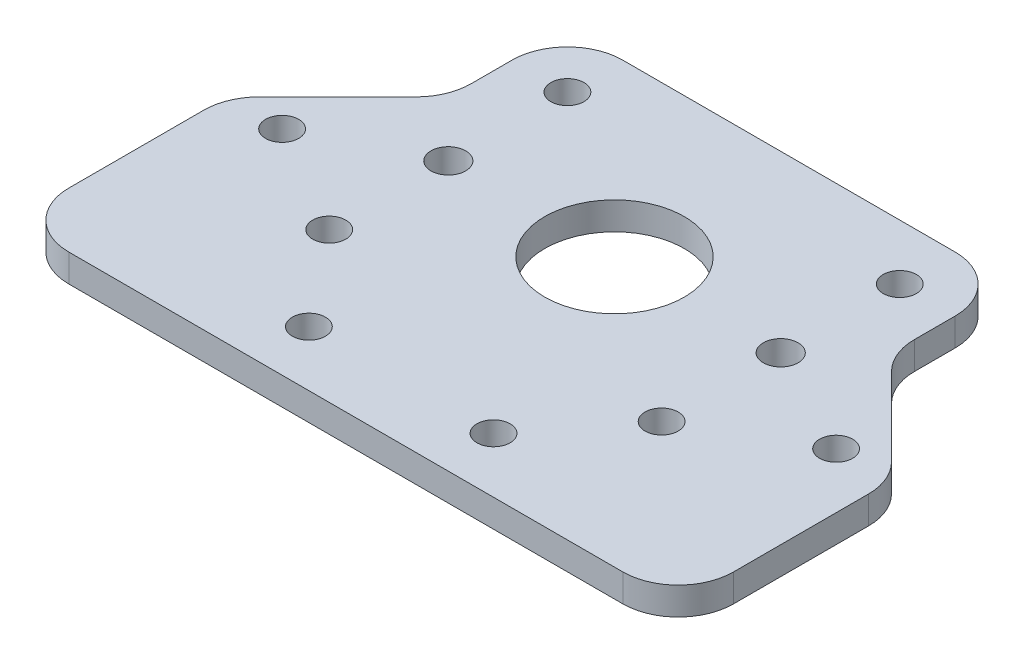
SolidWorks part; units mm, degrees
material "Balsa"
ref_plane "Front" through (0, 0, 0) normal (0, 0, 1) x (1, 0, 0)
ref_plane "Top" through (0, 0, 0) normal (0, 1, 0) x (1, 0, 0)
ref_plane "Right" through (0, 0, 0) normal (1, 0, 0) x (0, 0, -1)
sketch "Sketch1" plane through (0, 0, 0) normal (0, 1, 0) x (1, 0, 0)
  line L0 (38.1, 0) -> (38.1, 200) construction
  line L1 (0, 0) -> (76.2, 0)
  line L2 (0, 0) -> (0, 50.8)
  line L3 (0, 50.8) -> (38.1, 50.8)
  line L4 (38.1, 50.8) -> (76.2, 50.8)
  line L5 (38.1, 38.65) -> (79.051, 38.65) construction
  line L6 (38.1, 37.15) -> (79.051, 37.15) construction
  line L7 (76.2, 50.8) -> (76.2, 0)
  circle A0 centre (38.1, 118.65) radius 80 construction
  circle A1 centre (38.1, 30.8) radius 6.35 construction
  circle A2 centre (38.1, 30.8) radius 20 construction
  circle A4 centre (38.1, 30.8) radius 8
  dimension "D3" = 160
  dimension "D4" = 12.7
  dimension "D5" = 50.8
  dimension "D8" = 16
  dimension "D2" = 40
  dimension "D1" = 1.5
  dimension "D6" = 76.2
extrude "Boss-Extrude1" add sketch "Sketch1" along normal blind 3.175
sketch "Sketch2" plane through (0, 3.175, 0) normal (0, 1, 0) x (1, 0, 0)
  line L0 (38.1, 50.8) -> (38.1, 0) construction
  line L2 (0, 30.8) -> (76.2, 30.8) construction
  line L5 (76.2, 0) -> (76.2, 50.8) construction
  line L6 (76.2, 50.8) -> (0, 50.8) construction
  line L8 (0, 0) -> (76.2, 0) construction
  line L9 (0, 50.8) -> (0, 0) construction
  circle A1 centre (19.05, 30.8) radius 1.9939
  circle A4 centre (57.15, 30.8) radius 1.9939
  point P26 (38.1, 30.8)
  dimension "D1" = 3.9878
  dimension "D2" = 19.05
extrude "Cut-Extrude1" cut sketch "Sketch2" against normal through all
sketch "Sketch14" plane through (0, 0, 0) normal (0, -1, 0) x (1, 0, 0)
  line L0 (38.1, -30.8) -> (3.391, -30.8) construction
  line L2 (38.1, -30.8) -> (38.1, -33.65) construction
  line L3 (19.05, -17.15) -> (57.15, -17.15) construction
  line L5 (57.15, -44.45) -> (19.05, -44.45) construction
  line L7 (76.2, -50.8) -> (0, -50.8) construction
  line L8 (57.15, -30.8) -> (38.1, -30.8) construction
  circle A0 centre (38.1, -30.8) radius 8 construction
  circle A1 centre (57.15, -44.45) radius 1.8986
  circle A2 centre (19.05, -44.45) radius 1.8986
  circle A3 centre (19.05, -17.15) radius 1.8986
  circle A4 centre (57.15, -17.15) radius 1.8986
  circle A5 centre (57.15, -30.8) radius 1.9939 construction
  point P0 (57.15, -44.45)
  point P12 (19.05, -44.45)
  point P13 (19.05, -17.15)
  point P14 (57.15, -17.15)
  dimension "D3" = 3.7973
  dimension "D1" = 19.05
  dimension "D2" = 6.35
extrude "M3-tap" cut sketch "Sketch14" against normal through all
sketch "Sketch15" plane through (0, 0, 0) normal (0, -1, 0) x (1, 0, 0)
  line L0 (38.1, 0) -> (38.1, -48.7422) construction
  line L2 (76.2, 0) -> (76.2, -50.8) construction
  line L3 (0, 0) -> (76.2, 0) construction
  line L5 (76.2, -24.45) -> (69.85, -24.45) construction
  line L10 (69.85, -24.45) -> (69.85, 0) construction
  line L14 (69.85, -6.35) -> (48.6833, -6.35) construction
  line L15 (48.6833, -6.35) -> (27.5167, -6.35) construction
  line L16 (27.5167, -6.35) -> (6.35, -6.35) construction
  circle A0 centre (69.85, -24.45) radius 1.8987
  circle A1 centre (69.85, -6.35) radius 1.8987 construction
  circle A2 centre (48.6833, -6.35) radius 1.8986
  circle A3 centre (27.5167, -6.35) radius 1.8986
  circle A4 centre (6.35, -6.35) radius 1.8986 construction
  circle A5 centre (6.35, -24.45) radius 1.8986
  point P0 (69.85, -24.45)
  point P1 (69.85, -6.35)
  point P35 (6.35, -6.35)
  point P36 (6.35, -24.45)
  point P42 (48.6833, -6.35)
  point P50 (27.5167, -6.35)
  dimension "D4" = 3.7973
  dimension "D1" = 6.35
  dimension "D2" = 6.35
  dimension "D3" = 24.45
extrude "M5-through" cut sketch "Sketch15" against normal through all
sketch "Sketch12" plane through (0, 3.175, 0) normal (0, 1, 0) x (1, 0, 0)
  line L1 (0, 50.8) -> (12.7, 50.8)
  line L2 (0, 50.8) -> (0, 24.45)
  line L4 (12.7, 50.8) -> (12.7, 37.15)
  line L5 (38.1, 30.8) -> (38.1, 50.8) construction
  line L6 (76.2, 50.8) -> (0, 50.8) construction
  line L7 (63.5, 50.8) -> (63.5, 37.15)
  line L8 (76.2, 24.45) -> (63.5, 37.15)
  line L9 (76.2, 50.8) -> (76.2, 24.45)
  line L10 (76.2, 50.8) -> (63.5, 50.8)
  line L11 (12.7, 37.15) -> (0, 24.45)
  line L12 (0, 50.8) -> (0, 0) construction
  circle A1 centre (19.05, 44.45) radius 1.8987 construction
  dimension "D1" = 6.35
  dimension "D2" = 13.65
  dimension "D3" = 45
extrude "Cut-Extrude2" cut sketch "Sketch12" against normal through all
fillet "Fillet2" radius 6.35 8 edges at (76.2, 1.5875, 0) (0, 1.5875, 0) (76.2, 1.5875, -24.45) (63.5, 1.5875, -37.15) (63.5, 1.5875, -50.8) (12.7, 1.5875, -50.8) (0, 1.5875, -24.45) (12.7, 1.5875, -37.15)
sketch "Sketch13" [suppressed] plane through (0, 0, 0) normal (0, -1, 0) x (1, 0, 0)
  line L0 (69.85, -24.45) -> (69.85, -6.35) construction
  line L1 (69.85, -6.35) -> (6.35, -6.35) construction
  line L2 (6.35, -6.35) -> (6.35, -24.45) construction
  circle A0 centre (69.85, -15.4) radius 1.5
  circle A1 centre (38.1, -6.35) radius 1.5
  circle A2 centre (6.35, -15.4) radius 1.5
  dimension "D1" = 3
extrude "Cut-Extrude3" [suppressed] cut sketch "Sketch13" against normal through all
other "Move Face1" [suppressed] parameters "D1"=0.08
